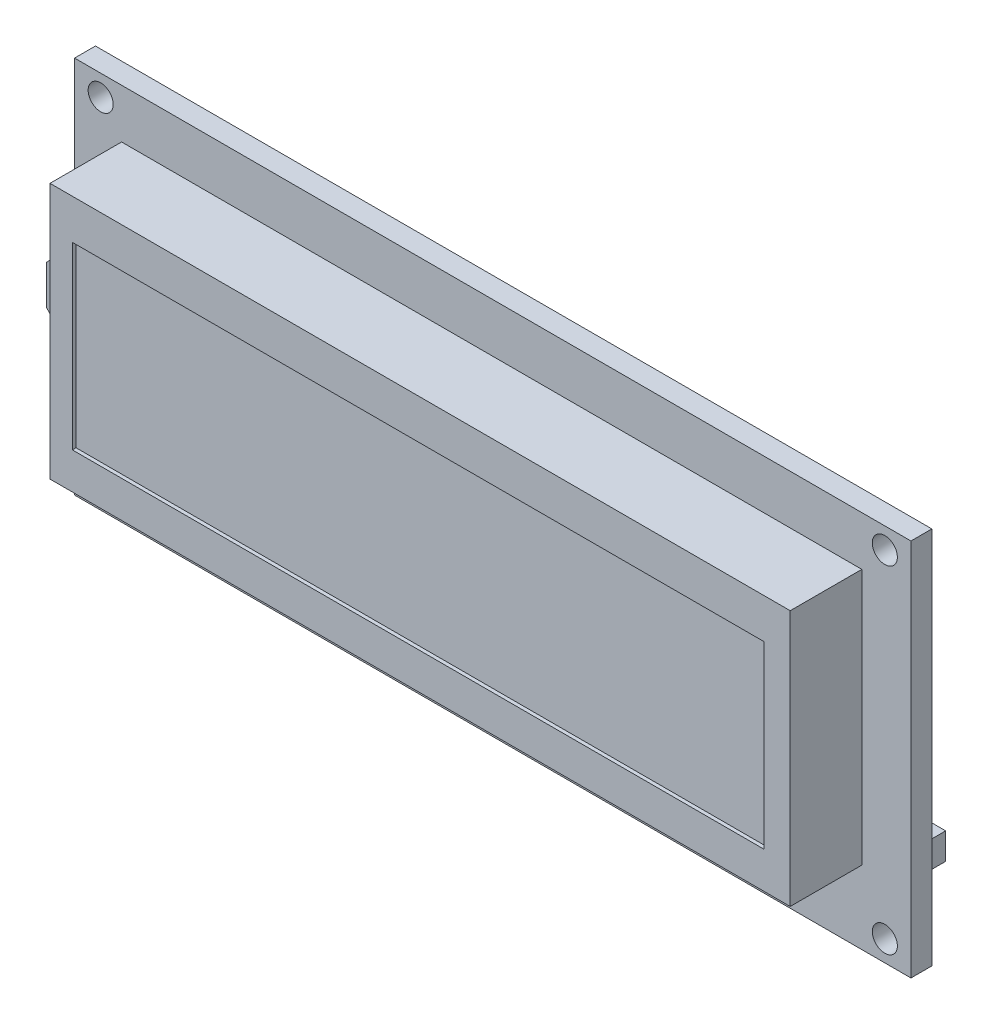
SolidWorks part; units mm, degrees
ref_plane "前视基准面" through (0, 0, 0) normal (0, 0, 1) x (1, 0, 0)
ref_plane "上视基准面" through (0, 0, 0) normal (0, 1, 0) x (1, 0, 0)
ref_plane "右视基准面" through (0, 0, 0) normal (1, 0, 0) x (0, 0, -1)
sketch "草图2" plane through (0, 0, 0) normal (0, 0, 1) x (1, 0, 0)
  line L1 (-74.092, 4.2616) -> (5.908, 4.2616)
  line L2 (-74.092, 4.2616) -> (-74.092, -31.9384)
  line L3 (-74.092, -31.9384) -> (5.908, -31.9384)
  line L4 (5.908, 4.2616) -> (5.908, -31.9384)
  circle A0 centre (3.408, -29.9384) radius 1.2
  circle A1 centre (-71.592, 2.2616) radius 1.2
  circle A2 centre (3.408, 2.2616) radius 1.2
  circle A3 centre (-71.592, -29.9384) radius 1.2
extrude "凸台-拉伸1" add sketch "草图2" along normal blind 2
sketch "草图3" plane through (0, 0, 0) normal (0, 0, 1) x (1, 0, 0)
  line L2 (-67.4545, -4.2534) -> (-1.3054, -4.2534)
  line L4 (-67.4545, -4.2534) -> (-67.4545, -21.4489)
  line L6 (-67.4545, -21.4489) -> (-1.3054, -21.4489)
  line L8 (-1.3054, -4.2534) -> (-1.3054, -21.4489)
  line L9 (-69.592, -0.4384) -> (1.208, -0.4384)
  line L10 (-69.592, -0.4384) -> (-69.592, -24.9384)
  line L11 (-69.592, -24.9384) -> (1.208, -24.9384)
  line L12 (1.208, -0.4384) -> (1.208, -24.9384)
extrude "凸台-拉伸2" add sketch "草图3" along normal blind 8.8497
sketch "草图4" plane through (0, 0, 2) normal (0, 0, 1) x (1, 0, 0)
  line L1 (-67.4545, -4.2534) -> (-1.3054, -4.2534)
  line L2 (-67.4545, -4.2534) -> (-67.4545, -21.4489)
  line L3 (-67.4545, -21.4489) -> (-1.3054, -21.4489)
  line L4 (-1.3054, -4.2534) -> (-1.3054, -21.4489)
extrude "凸台-拉伸3" add sketch "草图4" along normal blind 6.5 separate body
sketch "草图6" plane through (0, 0, 2) normal (0, 0, 1) x (1, 0, 0)
  line L0 (-4.6903, -29.2315) -> (-5.6903, -29.2315)
  line L1 (-1.092, -28.4084) -> (-42.092, -28.4084)
  line L2 (-1.092, -28.4084) -> (-1.092, -30.9384)
  line L3 (-1.092, -30.9384) -> (-42.092, -30.9384)
  line L4 (-42.092, -28.4084) -> (-42.092, -30.9384)
  line L6 (-2.1703, -29.2315) -> (-3.1703, -29.2315)
  line L8 (-2.1703, -29.2315) -> (-2.1703, -30.2315)
  line L9 (-2.1703, -30.2315) -> (-3.1703, -30.2315)
  line L10 (-3.1703, -29.2315) -> (-3.1703, -30.2315)
  line L11 (-4.6903, -29.2315) -> (-4.6903, -30.2315)
  line L12 (-4.6903, -30.2315) -> (-5.6903, -30.2315)
  line L13 (-5.6903, -29.2315) -> (-5.6903, -30.2315)
  line L14 (-7.2103, -29.2315) -> (-8.2103, -29.2315)
  line L15 (-7.2103, -29.2315) -> (-7.2103, -30.2315)
  line L16 (-7.2103, -30.2315) -> (-8.2103, -30.2315)
  line L17 (-8.2103, -29.2315) -> (-8.2103, -30.2315)
  line L18 (-9.7303, -29.2315) -> (-10.7303, -29.2315)
  line L19 (-9.7303, -29.2315) -> (-9.7303, -30.2315)
  line L20 (-9.7303, -30.2315) -> (-10.7303, -30.2315)
  line L21 (-10.7303, -29.2315) -> (-10.7303, -30.2315)
  line L22 (-12.2503, -29.2315) -> (-13.2503, -29.2315)
  line L23 (-12.2503, -29.2315) -> (-12.2503, -30.2315)
  line L24 (-12.2503, -30.2315) -> (-13.2503, -30.2315)
  line L25 (-13.2503, -29.2315) -> (-13.2503, -30.2315)
  line L26 (-14.7703, -29.2315) -> (-15.7703, -29.2315)
  line L27 (-14.7703, -29.2315) -> (-14.7703, -30.2315)
  line L28 (-14.7703, -30.2315) -> (-15.7703, -30.2315)
  line L29 (-15.7703, -29.2315) -> (-15.7703, -30.2315)
  line L30 (-17.2903, -29.2315) -> (-18.2903, -29.2315)
  line L31 (-17.2903, -29.2315) -> (-17.2903, -30.2315)
  line L32 (-17.2903, -30.2315) -> (-18.2903, -30.2315)
  line L33 (-18.2903, -29.2315) -> (-18.2903, -30.2315)
  line L34 (-19.8103, -29.2315) -> (-20.8103, -29.2315)
  line L35 (-19.8103, -29.2315) -> (-19.8103, -30.2315)
  line L36 (-19.8103, -30.2315) -> (-20.8103, -30.2315)
  line L37 (-20.8103, -29.2315) -> (-20.8103, -30.2315)
  line L38 (-22.3303, -29.2315) -> (-23.3303, -29.2315)
  line L39 (-22.3303, -29.2315) -> (-22.3303, -30.2315)
  line L40 (-22.3303, -30.2315) -> (-23.3303, -30.2315)
  line L41 (-23.3303, -29.2315) -> (-23.3303, -30.2315)
  line L42 (-24.8503, -29.2315) -> (-25.8503, -29.2315)
  line L43 (-24.8503, -29.2315) -> (-24.8503, -30.2315)
  line L44 (-24.8503, -30.2315) -> (-25.8503, -30.2315)
  line L45 (-25.8503, -29.2315) -> (-25.8503, -30.2315)
  line L46 (-27.3703, -29.2315) -> (-28.3703, -29.2315)
  line L47 (-27.3703, -29.2315) -> (-27.3703, -30.2315)
  line L48 (-27.3703, -30.2315) -> (-28.3703, -30.2315)
  line L49 (-28.3703, -29.2315) -> (-28.3703, -30.2315)
  line L50 (-29.8903, -29.2315) -> (-30.8903, -29.2315)
  line L51 (-29.8903, -29.2315) -> (-29.8903, -30.2315)
  line L52 (-29.8903, -30.2315) -> (-30.8903, -30.2315)
  line L53 (-30.8903, -29.2315) -> (-30.8903, -30.2315)
  line L54 (-32.4103, -29.2315) -> (-33.4103, -29.2315)
  line L55 (-32.4103, -29.2315) -> (-32.4103, -30.2315)
  line L56 (-32.4103, -30.2315) -> (-33.4103, -30.2315)
  line L57 (-33.4103, -29.2315) -> (-33.4103, -30.2315)
  line L58 (-34.9303, -29.2315) -> (-35.9303, -29.2315)
  line L59 (-34.9303, -29.2315) -> (-34.9303, -30.2315)
  line L60 (-34.9303, -30.2315) -> (-35.9303, -30.2315)
  line L61 (-35.9303, -29.2315) -> (-35.9303, -30.2315)
  line L62 (-37.4503, -29.2315) -> (-38.4503, -29.2315)
  line L63 (-37.4503, -29.2315) -> (-37.4503, -30.2315)
  line L64 (-37.4503, -30.2315) -> (-38.4503, -30.2315)
  line L65 (-38.4503, -29.2315) -> (-38.4503, -30.2315)
  line L66 (-39.9703, -29.2315) -> (-40.9703, -29.2315)
  line L67 (-39.9703, -29.2315) -> (-39.9703, -30.2315)
  line L68 (-39.9703, -30.2315) -> (-40.9703, -30.2315)
  line L69 (-40.9703, -29.2315) -> (-40.9703, -30.2315)
  dimension "D1" = 16
extrude "凸台-拉伸4" add sketch "草图6" against normal blind 10.32
sketch "草图7" plane through (0, 0, 2) normal (0, 0, 1) x (1, 0, 0)
  line L0 (-74.092, 4.2616) -> (-74.092, -31.9384) construction
  line L2 (-69.592, -19.4384) -> (-69.592, -6.4384)
  line L11 (-69.592, -19.4384) -> (-74.092, -15.0458)
  line L12 (-74.092, -15.0458) -> (-74.092, -11.3241)
  line L13 (-74.092, -11.3241) -> (-69.592, -6.4384)
extrude "凸台-拉伸5" add sketch "草图7" along normal blind 2.7
sketch "草图8" plane through (0, 0, 0) normal (0, 0, -1) x (-1, 0, 0)
  line L0 (30.2104, -2.1142) -> (30.2104, -5.323)
  line L1 (2.2104, -2.1142) -> (9.5329, -2.1142)
  line L2 (2.2104, -2.1142) -> (2.2104, -5.323)
  line L3 (2.2104, -5.323) -> (9.5329, -5.323)
  line L4 (9.5329, -2.1142) -> (9.5329, -5.323)
  line L5 (30.2104, -2.1142) -> (37.5329, -2.1142)
  line L6 (37.5329, -2.1142) -> (37.5329, -5.323)
  line L7 (30.2104, -5.323) -> (37.5329, -5.323)
  line L8 (58.2104, -2.1142) -> (58.2104, -5.323)
  line L9 (58.2104, -2.1142) -> (65.5329, -2.1142)
  line L10 (65.5329, -2.1142) -> (65.5329, -5.323)
  line L11 (58.2104, -5.323) -> (65.5329, -5.323)
  line L12 (30.2104, -22.1142) -> (30.2104, -25.323)
  line L13 (30.2104, -22.1142) -> (37.5329, -22.1142)
  line L14 (37.5329, -22.1142) -> (37.5329, -25.323)
  line L15 (30.2104, -25.323) -> (37.5329, -25.323)
  line L16 (58.2104, -22.1142) -> (58.2104, -25.323)
  line L17 (58.2104, -22.1142) -> (65.5329, -22.1142)
  line L18 (65.5329, -22.1142) -> (65.5329, -25.323)
  line L19 (58.2104, -25.323) -> (65.5329, -25.323)
  line L20 (2.2104, -22.1142) -> (2.2104, -25.323)
  line L21 (2.2104, -22.1142) -> (9.5329, -22.1142)
  line L22 (9.5329, -22.1142) -> (9.5329, -25.323)
  line L23 (2.2104, -25.323) -> (9.5329, -25.323)
  dimension "D1" = 2
extrude "凸台-拉伸6" add sketch "草图8" along normal blind 2.5
